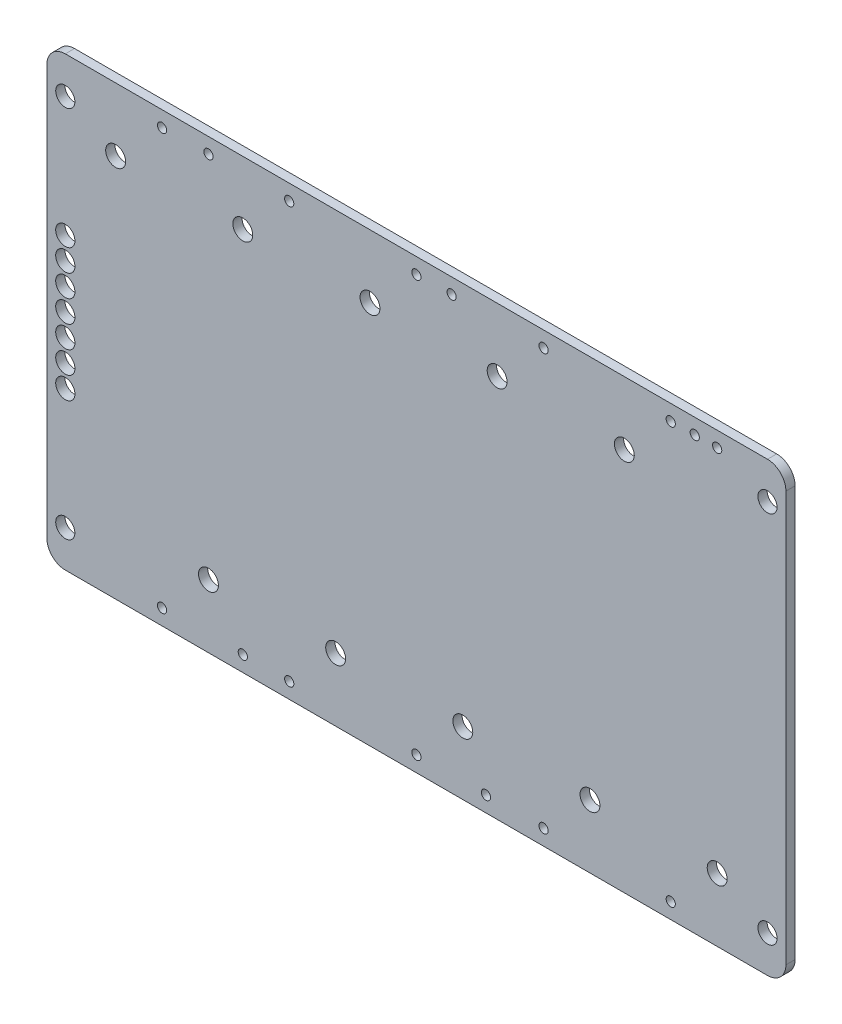
SolidWorks part; units mm, degrees
ref_plane "Front Plane" through (0, 0, 0) normal (0, 0, 1) x (1, 0, 0)
ref_plane "Top Plane" through (0, 0, 0) normal (0, 1, 0) x (1, 0, 0)
ref_plane "Right Plane" through (0, 0, 0) normal (1, 0, 0) x (0, 0, -1)
sketch "Sketch1" plane through (0, 0, 0) normal (0, 0, 1) x (1, 0, 0)
  line L0 (21.9202, 77.0636) -> (21.9202, 0) construction
  line L1 (0, 0) -> (117.856, 0)
  line L2 (0, 0) -> (0, 77.0636) construction
  line L3 (0, 77.0636) -> (117.856, 77.0636)
  line L4 (117.856, 77.0636) -> (117.856, 0)
  line L5 (20.6502, 77.0636) -> (20.6502, 0) construction
  line L6 (10.3251, 74.3712) -> (0, 74.3712) construction
  line L7 (10.3251, 74.3712) -> (20.6502, 74.3712) construction
  line L8 (10.3251, 2.6924) -> (10.3251, 0) construction
  line L9 (10.3251, 74.3712) -> (10.3251, 77.0636) construction
  line L10 (18.3261, 66.1543) -> (20.6502, 66.1543) construction
  line L11 (2.3241, 66.1543) -> (0, 66.1543) construction
  line L12 (18.3261, 10.9093) -> (20.6502, 10.9093) construction
  line L13 (42.5704, 77.0636) -> (42.5704, 0) construction
  line L14 (18.3261, 66.1543) -> (18.3261, 77.0636) construction
  line L15 (18.3261, 10.9093) -> (18.3261, 0) construction
  line L16 (21.9202, 66.1543) -> (24.2443, 66.1543) construction
  line L17 (42.5704, 66.1543) -> (36.2579, 66.1543) construction
  line L18 (42.5704, 74.3712) -> (21.9202, 74.3712) construction
  line L19 (32.2453, 74.3712) -> (32.2453, 77.0636) construction
  line L20 (32.2453, 0) -> (32.2453, 2.6924) construction
  line L21 (0, 77.0636) -> (-9.525, 77.0636)
  line L22 (-9.525, 77.0636) -> (-9.525, 0)
  line L23 (-9.525, 0) -> (0, 0)
  line L24 (42.5704, 10.9093) -> (40.2463, 10.9093) construction
  line L25 (42.5704, 2.6924) -> (32.2453, 2.6924) construction
  line L26 (86.4108, 77.0636) -> (86.4108, 0) construction
  line L27 (-6.35, 70.7136) -> (-6.35, 77.0636) construction
  line L28 (-6.35, 6.35) -> (-6.35, 0) construction
  line L29 (65.7606, 77.0636) -> (65.7606, 0) construction
  line L30 (64.4906, 77.0636) -> (64.4906, 0) construction
  line L31 (43.8404, 0) -> (43.8404, 77.0636) construction
  line L32 (-6.35, 70.7136) -> (114.681, 70.7136) construction
  line L34 (108.331, 77.0636) -> (108.331, 0) construction
  line L35 (87.6808, 0) -> (87.6808, 77.0636) construction
  line L36 (42.5704, 77.0636) -> (86.4108, 77.0636) construction
  line L37 (114.681, 77.0636) -> (114.681, 70.7136) construction
  line L38 (114.681, 0) -> (114.681, 6.35) construction
  line L39 (21.9202, 2.6924) -> (24.2443, 2.6924) construction
  line L40 (24.2443, 2.6924) -> (66.1543, 2.6924) construction
  line L42 (-6.35, 38.5318) -> (-9.525, 38.5318) construction
  line L43 (-6.35, 38.5318) -> (-6.35, 42.3418) construction
  line L44 (109.601, 77.0636) -> (109.601, 0) construction
  line L45 (130.2512, 77.0636) -> (130.2512, 0) construction
  circle A0 centre (10.3251, 74.3712) radius 0.7937
  circle A1 centre (10.3251, 2.6924) radius 0.7937
  circle A2 centre (2.3241, 66.1543) radius 1.7145
  circle A3 centre (18.3261, 74.4347) radius 0.7937
  circle A4 centre (18.3261, 10.9093) radius 1.7145
  circle A5 centre (24.2443, 66.1543) radius 1.7145
  circle A6 centre (32.2453, 74.3712) radius 0.7937
  circle A7 centre (32.2453, 2.6924) radius 0.7937
  circle A8 centre (40.2463, 10.9093) radius 1.7145
  circle A9 centre (32.2453, 2.6924) radius 0.7937
  circle A10 centre (68.0847, 66.1543) radius 1.7145
  circle A11 centre (76.0857, 2.6924) radius 0.7937
  circle A12 centre (76.0857, 2.6924) radius 0.7937
  circle A13 centre (84.0867, 10.9093) radius 1.7145
  circle A14 centre (76.0857, 74.3712) radius 0.7937
  circle A15 centre (66.1543, 2.6924) radius 0.7937
  circle A16 centre (54.1655, 74.3712) radius 0.7937
  circle A17 centre (46.1645, 66.1543) radius 1.7145
  circle A18 centre (-6.35, 70.7136) radius 1.651
  circle A19 centre (-6.35, 6.35) radius 1.651
  circle A20 centre (62.1665, 10.9093) radius 1.7145
  circle A21 centre (54.1655, 2.6924) radius 0.7937
  circle A26 centre (60.2361, 74.4347) radius 0.7937
  circle A27 centre (106.0069, 74.4347) radius 0.7937
  circle A28 centre (98.0059, 74.3712) radius 0.7937
  circle A29 centre (90.0049, 66.1543) radius 1.7145
  circle A30 centre (106.0069, 10.9093) radius 1.7145
  circle A31 centre (98.0059, 2.6924) radius 0.7937
  circle A32 centre (114.681, 70.7136) radius 1.651
  circle A33 centre (114.681, 6.35) radius 1.651
  circle A34 centre (24.2443, 2.6924) radius 0.7937
  circle A35 centre (62.1665, 74.4347) radius 0.7937 [skipped]
  circle A36 centre (119.9261, 74.3712) radius 0.7937 [skipped]
  circle A38 centre (102.1461, 74.4347) radius 0.7937
  circle A40 centre (-6.35, 38.5318) radius 1.6593
  circle A41 centre (-6.35, 42.3418) radius 1.6593
  circle A42 centre (-6.35, 46.1518) radius 1.6593
  circle A43 centre (-6.35, 49.9618) radius 1.6593
  circle A44 centre (-6.35, 38.5318) radius 1.6593
  circle A45 centre (-6.35, 42.3418) radius 1.6593
  circle A46 centre (-6.35, 46.1518) radius 1.6593
  circle A47 centre (-6.35, 34.7218) radius 1.6593
  circle A48 centre (-6.35, 38.5318) radius 1.6593
  circle A49 centre (-6.35, 42.3418) radius 1.6593
  circle A50 centre (-6.35, 30.9118) radius 1.6593
  circle A51 centre (-6.35, 34.7218) radius 1.6593
  circle A52 centre (-6.35, 38.5318) radius 1.6593
  circle A53 centre (-6.35, 34.7218) radius 1.6593
  circle A54 centre (-6.35, 30.9118) radius 1.6593
  circle A55 centre (-6.35, 27.1018) radius 1.6593
  circle A56 centre (127.9271, 10.9093) radius 1.7145 [skipped]
  circle A57 centre (119.9261, 2.6924) radius 0.7937 [skipped]
  circle A58 centre (108.0643, 2.6924) radius 0.7937 [skipped]
  circle A59 centre (111.9251, 66.1543) radius 1.7145 [skipped]
  circle A60 centre (119.9261, 2.6924) radius 0.7937 [skipped]
  dimension "D6" = 1.5875
  dimension "D7" = 3.429
  dimension "D13" = 3.302
  dimension "D15" = 20.6502
  dimension "D11" = 1.5875
  dimension "D16" = 3
  dimension "D18" = 1.27
  dimension "D24" = 3.3186
  dimension "D1" = 77.0636
  dimension "D3" = 20.6502
  dimension "D4" = 1.27
  dimension "D5" = 71.6788
  dimension "D8" = 16.002
  dimension "D9" = 55.245
  dimension "D10" = 8.2804
  dimension "D12" = 3.175
  dimension "D14" = 6.35
  dimension "D17" = 3
  dimension "D19" = 71.6788
  dimension "D20" = 3.175
  dimension "D21" = 41.91
  dimension "D23" = 121.031
  dimension "D27" = 3.81
  dimension "D22" = 6.35
  dimension "D28" = 6.35
  dimension "D25" = 4
  dimension "D26" = 4
extrude "Boss-Extrude1" add sketch "Sketch1" along normal blind 1.5875
fillet "Fillet1" radius 3.175 4 edges at (-9.525, 0, 0.7937) (117.856, 0, 0.7937) (117.856, 77.0636, 0.7937) (-9.525, 77.0636, 0.7937)
